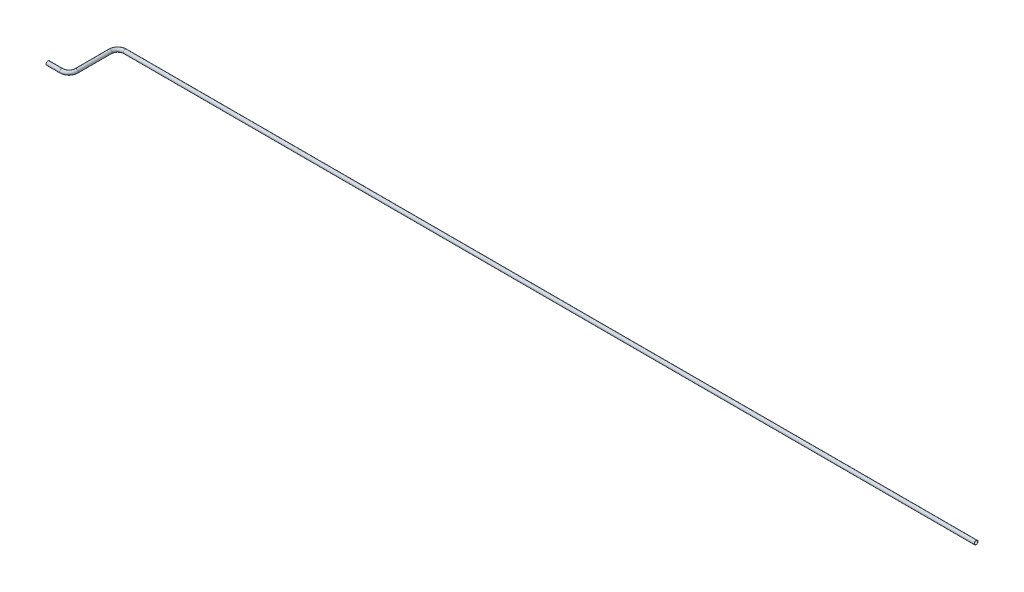
SolidWorks part; units mm, degrees
material "AISI Type 316L stainless steel"
ref_plane "Front Plane" through (0, 0, 0) normal (0, 0, 1) x (1, 0, 0)
ref_plane "Top Plane" through (0, 0, 0) normal (0, 1, 0) x (1, 0, 0)
ref_plane "Right Plane" through (0, 0, 0) normal (1, 0, 0) x (0, 0, -1)
sketch3d "3DSketch1"
  line L1 (0, 0, 0) -> (22.86, 0, 0)
  line L2 (35.56, 0, -12.7) -> (35.56, 0, -69.4883)
  line L3 (48.26, 0, -82.1883) -> (1483.36, 0, -82.1883)
  arc A1 (35.56, 0, -69.4883) -> (48.26, 0, -82.1883) centre (48.26, 0, -69.4883) ccw
  arc A2 (22.86, 0, 0) -> (35.56, 0, -12.7) centre (22.86, 0, -12.7) ccw
  point P16 (35.56, 0, -82.1883)
  point P17 (48.26, -12.7, -69.4883)
  point P20 (35.56, 0, 0)
  point P22 (22.86, 12.7, -12.7)
  dimension "D7" = 12.7
  dimension "D1" = 35.56
  dimension "D2" = 82.1883
  dimension "D3" = 1447.8
ref_plane "Plane4" through (0, 0, 0) normal (1, 0, 0) x (0, 0, -1)
sketch "Sketch5" plane through (0, 0, 0) normal (1, 0, 0) x (0, 0, -1)
  circle A0 centre (0, 0) radius 3.175
  circle A1 centre (0, 0) radius 2.667
  dimension "D1" = 6.35
  dimension "D2" = 0.508
sweep "Sweep3" add profiles "Sketch5" path "3DSketch1"
